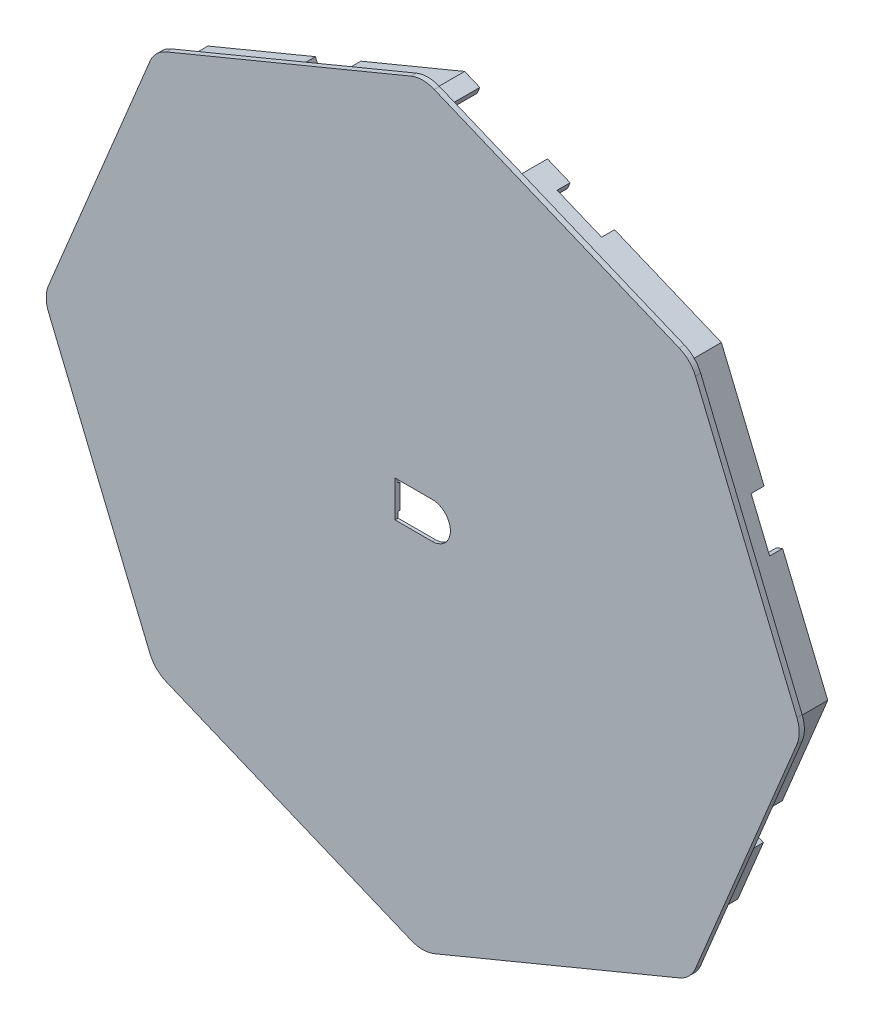
SolidWorks part; units mm, degrees
ref_plane "Plan de face" through (0, 0, 0) normal (0, 0, 1) x (1, 0, 0)
ref_plane "Plan de dessus" through (0, 0, 0) normal (0, 1, 0) x (1, 0, 0)
ref_plane "Plan de droite" through (0, 0, 0) normal (1, 0, 0) x (0, 0, -1)
sketch "Esquisse1" plane through (0, 0, 0) normal (0, 0, 1) x (1, 0, 0)
  line L0 (-19.5173, 52.6223) -> (-47.8358, 40.8923)
  line L5 (-49.73, 38.9982) -> (-61.46, 10.6796)
  line L6 (-61.46, 8.0008) -> (-49.73, -20.3178)
  line L7 (-47.8358, -22.212) -> (-19.5173, -33.9419)
  line L8 (-16.8385, -33.9419) -> (11.4801, -22.212)
  line L9 (13.3743, -20.3178) -> (25.1042, 8.0008)
  line L10 (25.1042, 10.6796) -> (13.3743, 38.9982)
  line L11 (11.4801, 40.8923) -> (-16.8385, 52.6223)
  arc A0 (-47.8358, 40.8923) -> (-49.73, 38.9982) centre (-46.4964, 37.6588) ccw
  arc A1 (-61.46, 10.6796) -> (-61.46, 8.0008) centre (-58.2264, 9.3402) ccw
  arc A2 (-49.73, -20.3178) -> (-47.8358, -22.212) centre (-46.4964, -18.9784) ccw
  arc A3 (-19.5173, -33.9419) -> (-16.8385, -33.9419) centre (-18.1779, -30.7083) ccw
  arc A4 (11.4801, -22.212) -> (13.3743, -20.3178) centre (10.1407, -18.9784) ccw
  arc A5 (25.1042, 8.0008) -> (25.1042, 10.6796) centre (21.8706, 9.3402) ccw
  arc A6 (13.3743, 38.9982) -> (11.4801, 40.8923) centre (10.1407, 37.6588) ccw
  arc A7 (-16.8385, 52.6223) -> (-19.5173, 52.6223) centre (-18.1779, 49.3887) ccw
extrude "Boss.-Extru.1" add sketch "Esquisse1" along normal blind 0.6
sketch "Esquisse3" plane through (0, 0, 0) normal (0, 0, -1) x (-1, 0, 0)
  line L63 (47.2618, 38.4241) -> (18.1779, 50.4711)
  line L64 (18.1779, 50.4711) -> (-10.9061, 38.4241)
  line L65 (-10.9061, 38.4241) -> (-22.953, 9.3402)
  line L66 (-22.953, 9.3402) -> (-10.9061, -19.7437)
  line L67 (-10.9061, -19.7437) -> (18.1779, -31.7907)
  line L68 (18.1779, -31.7907) -> (47.2618, -19.7437)
  line L69 (47.2618, -19.7437) -> (59.3088, 9.3402)
  line L70 (59.3088, 9.3402) -> (47.2618, 38.4241)
  line L71 (47.8741, 39.0364) -> (18.1779, 51.337)
  line L72 (60.1747, 9.3402) -> (47.8741, 39.0364)
  line L73 (47.8741, -20.356) -> (60.1747, 9.3402)
  line L74 (18.1779, -32.6566) -> (47.8741, -20.356)
  line L75 (-11.5184, -20.356) -> (18.1779, -32.6566)
  line L76 (-23.8189, 9.3402) -> (-11.5184, -20.356)
  line L77 (-11.5184, 39.0364) -> (-23.8189, 9.3402)
  line L78 (18.1779, 51.337) -> (-11.5184, 39.0364)
  line L79 (47.8741, 39.0364) -> (18.1779, 51.337)
  line L80 (60.1747, 9.3402) -> (47.8741, 39.0364)
  line L81 (47.8741, -20.356) -> (60.1747, 9.3402)
  line L82 (18.1779, -32.6566) -> (47.8741, -20.356)
  line L83 (-11.5184, -20.356) -> (18.1779, -32.6566)
  line L84 (-23.8189, 9.3402) -> (-11.5184, -20.356)
  line L85 (-11.5184, 39.0364) -> (-23.8189, 9.3402)
  line L86 (18.1779, 51.337) -> (-11.5184, 39.0364)
  dimension "D1" = 0.2
  dimension "D2" = 0.8
extrude "Boss.-Extru.2" add sketch "Esquisse3" along normal blind 4.25
sketch "Esquisse4" plane through (0, 0, 0) normal (0, 0, -1) x (-1, 0, 0)
  line L0 (17.7779, 6.6402) -> (17.7779, 12.0402) construction
  line L6 (21.1779, 6.6402) -> (14.3779, 6.6402) construction
  line L7 (14.3779, 12.0402) -> (21.1779, 12.0402) construction
  line L8 (14.3779, 6.6402) -> (14.3779, 12.0402) construction
  line L9 (21.3779, 6.4402) -> (14.1779, 6.4402)
  line L10 (21.3779, 6.4402) -> (21.3779, 12.2402)
  line L11 (21.3779, 12.2402) -> (14.1779, 12.2402)
  line L12 (14.1779, 6.4402) -> (14.1779, 12.2402)
  line L13 (21.3779, 6.4402) -> (14.1779, 12.2402) construction
  line L14 (21.3779, 12.2402) -> (14.1779, 6.4402) construction
  point P6 (17.7779, 9.3402)
  dimension "D1" = 0.2
  dimension "D2" = 0.2
extrude "Enlèv. mat.-Extru.2" cut sketch "Esquisse4" against normal blind 0.25
sketch "Esquisse2" plane through (0, 0, 0.6) normal (0, 0, 1) x (1, 0, 0)
  line L0 (-18.1779, -34.2083) -> (-18.1779, 52.8887) construction
  line L1 (-14.9779, 9.3402) -> (-21.3779, 9.3402) construction
  line L8 (-21.3779, 11.4402) -> (-17.0779, 11.4402)
  line L13 (-21.3779, 7.2402) -> (-17.0779, 7.2402)
  line L14 (-21.3779, 11.4402) -> (-21.3779, 7.2402)
  arc A0 (-19.5173, -33.9419) -> (-16.8385, -33.9419) centre (-18.1779, -30.7083) ccw construction
  arc A1 (-16.8385, 52.6223) -> (-19.5173, 52.6223) centre (-18.1779, 49.3887) ccw construction
  arc A9 (-17.0779, 11.4402) -> (-17.0779, 7.2402) centre (-17.0779, 9.3402) cw
extrude "Enlèv. mat.-Extru.1" cut sketch "Esquisse2" against normal blind 1
sketch "Esquisse5" plane through (15.4883, 37.392, 0) normal (0.3827, 0.9239, 0) x (0.9239, -0.3827, 0)
  line L1 (-26.0698, 0) -> (-34.542, 0)
  line L2 (-26.0698, 0) -> (-26.0698, 4.25)
  line L3 (-26.0698, 4.25) -> (-34.542, 4.25)
  line L4 (-34.542, 0) -> (-34.542, 4.25)
  line L5 (-36.44, 4.25) -> (-4.297, 4.25) construction
extrude "Enlèv. mat.-Extru.3" cut sketch "Esquisse5" against normal blind 1
sketch "Esquisse7" plane through (0, 0, -4.25) normal (0, 0, -1) x (-1, 0, 0)
  line L0 (-17.505, 21.4789) -> (-15.3414, 26.6549)
  line L1 (-17.505, 21.4789) -> (-18.939, 22.0784)
  line L2 (-15.3414, 26.6549) -> (-16.7754, 27.2543)
  line L3 (-18.939, 22.0784) -> (-16.7754, 27.2543)
  line L4 (-17.505, 21.4789) -> (-16.7754, 27.2543) construction
  line L5 (-15.3414, 26.6549) -> (-18.939, 22.0784) construction
  line L6 (18.1779, -33.7083) -> (18.1779, 52.3887) construction
  line L7 (-15.6405, -8.3138) -> (-17.8205, -3.0508)
  line L8 (-22.953, 9.3402) -> (-10.9061, -19.7437) construction
  line L9 (-17.8205, -3.0508) -> (-18.5596, -3.357)
  line L10 (-23.8189, 9.3402) -> (-11.5184, -20.356) construction
  line L11 (-18.5596, -3.357) -> (-16.3796, -8.6199)
  line L12 (-16.3796, -8.6199) -> (-15.6405, -8.3138)
  line L13 (6.6989, -27.036) -> (6.3928, -27.7751)
  line L14 (-10.9061, -19.7437) -> (18.1779, -31.7907) construction
  line L15 (-11.5184, -20.356) -> (18.1779, -32.6566) construction
  line L16 (6.3928, -27.7751) -> (1.1822, -25.6168)
  line L17 (1.1822, -25.6168) -> (1.4883, -24.8777)
  line L18 (1.4883, -24.8777) -> (6.6989, -27.036)
  line L19 (35.0484, -24.8027) -> (29.6568, -27.036)
  line L20 (18.1779, -31.7907) -> (47.2618, -19.7437) construction
  line L21 (29.6568, -27.036) -> (29.963, -27.7751)
  line L22 (18.1779, -32.6566) -> (47.8741, -20.356) construction
  line L23 (29.963, -27.7751) -> (35.3546, -25.5418)
  line L24 (35.3546, -25.5418) -> (35.0484, -24.8027)
  line L25 (52.1789, -7.8728) -> (52.918, -8.1789)
  line L26 (47.2618, -19.7437) -> (59.3088, 9.3402) construction
  line L27 (47.8741, -20.356) -> (60.1747, 9.3402) construction
  line L28 (52.918, -8.1789) -> (55.13, -2.8387)
  line L29 (55.13, -2.8387) -> (54.3909, -2.5326)
  line L30 (54.3909, -2.5326) -> (52.1789, -7.8728)
  line L31 (54.3213, 21.381) -> (55.0604, 21.6871)
  line L32 (59.3088, 9.3402) -> (47.2618, 38.4241) construction
  line L33 (60.1747, 9.3402) -> (47.8741, 39.0364) construction
  line L34 (55.0604, 21.6871) -> (52.8956, 26.9135)
  line L35 (52.8956, 26.9135) -> (52.1565, 26.6074)
  line L36 (52.1565, 26.6074) -> (54.3213, 21.381)
  line L37 (29.88, 45.6239) -> (30.1861, 46.363)
  line L38 (47.2618, 38.4241) -> (18.1779, 50.4711) construction
  line L39 (47.8741, 39.0364) -> (18.1779, 51.337) construction
  line L40 (30.1861, 46.363) -> (35.4331, 44.1896)
  line L41 (35.4331, 44.1896) -> (35.127, 43.4505)
  line L42 (35.127, 43.4505) -> (29.88, 45.6239)
  line L43 (6.2864, 45.5455) -> (5.9803, 46.2846)
  line L44 (8.9032, 46.6294) -> (-10.9061, 38.4241) construction
  line L45 (8.597, 47.3685) -> (-11.5184, 39.0364) construction
  line L46 (5.9803, 46.2846) -> (0.8379, 44.1546)
  line L47 (0.8379, 44.1546) -> (1.1441, 43.4155)
  line L48 (1.1441, 43.4155) -> (6.2864, 45.5455)
  point P1 (-17.1402, 24.3666)
  point P13 (18.1779, 9.3402)
extrude "Enlèv. mat.-Extru.4" cut sketch "Esquisse7" against normal blind 1.5
ref_plane "Plan1" through (16.846, -16.846, 0) normal (-0.7071, 0.7071, 0) x (0, 0, 1)
sketch "Esquisse8" plane through (16.846, -16.846, 0) normal (-0.7071, 0.7071, 0) x (0, 0, 1)
  line L6 (-0.2158, -1.666) -> (-4.45, -1.666)
  line L7 (-4.45, -10.766) -> (-4.45, -1.666)
  line L8 (-0.2158, -10.766) -> (-4.45, -10.766)
  line L9 (-0.2158, -10.766) -> (-0.2158, -1.666)
extrude "Enlèv. mat.-Extru.5" cut sketch "Esquisse8" along normal blind 5
sketch "Esquisse9" plane through (0, 0, -10) normal (0, 0, -1) x (-1, 0, 0)
  line L0 (-95.335, 117.5946) -> (-278.1174, 117.5946) construction
  line L1 (18.1779, -34.2495) -> (18.1779, 52.9299) construction
  line L2 (-25.4118, 9.3402) -> (61.7676, 9.3402) construction
  line L3 (-10.375, 4.3056) -> (-0.9298, 4.9699)
  line L4 (0, 5.9674) -> (0, 12.713)
  line L5 (-8.3173, -1.6814) -> (-1.1982, -0.2422)
  line L6 (0, -1.2224) -> (0, -12.2881)
  line L7 (15.377, 12.2209) -> (15.377, 6.4595)
  line L8 (0, 9.3402) -> (1.6274, 9.3402)
  line L9 (1.6274, 29.788) -> (1.6274, -11.1076)
  line L10 (1.9689, -11.8602) -> (2.4106, -12.2467)
  line L11 (3.8901, -12.065) -> (10.0273, -3.2398)
  line L12 (10.2064, -2.6689) -> (10.2064, 21.3493)
  line L13 (44.603, 5.5333) -> (7.788, -15.7985)
  line L14 (43.8776, 8.2733) -> (32.8856, 8.5506)
  line L15 (32.3569, 8.4149) -> (11.7348, -3.602)
  line L16 (11.3684, -3.9729) -> (5.8348, -13.7345)
  line L17 (17.1266, 5.3032) -> (21.1779, 8.2763)
  line L18 (21.1779, 12.0402) -> (21.1779, 6.6402) construction
  line L19 (36.6565, -1.0939) -> (45.9203, 3.9638)
  line L20 (36.3722, -2.6175) -> (40.9733, -8.0556)
  line L21 (30.0138, -4.7878) -> (24.1751, -8.1284)
  line L22 (23.7662, -9.4207) -> (27.7907, -18.0089)
  line L23 (31.325, -5.0757) -> (36.8392, -12.8188)
  line L24 (8.4389, -17.1929) -> (17.9866, -11.5351)
  line L25 (19.4327, -12.0443) -> (22.0647, -19.0641)
  line L26 (19.4327, 30.7247) -> (22.0647, 37.7445)
  line L27 (8.4389, 35.8733) -> (17.9866, 30.2155)
  line L28 (31.325, 23.7561) -> (36.8392, 31.4992)
  line L29 (23.7662, 28.1011) -> (27.7907, 36.6893)
  line L30 (30.0138, 23.4682) -> (24.1751, 26.8088)
  line L31 (36.3722, 21.2979) -> (40.9733, 26.736)
  line L32 (36.6565, 19.7743) -> (45.9203, 14.7166)
  line L33 (17.1266, 13.3772) -> (21.1779, 10.4041)
  line L34 (11.3684, 22.6533) -> (5.8348, 32.4149)
  line L35 (32.3569, 10.2655) -> (11.7348, 22.2824)
  line L36 (43.8776, 10.407) -> (32.8856, 10.1298)
  line L37 (44.603, 13.1471) -> (7.788, 34.4788)
  line L38 (3.8901, 30.7454) -> (10.0273, 21.9202)
  line L39 (1.9689, 30.5406) -> (2.4106, 30.9271)
  line L40 (0, 19.9028) -> (0, 30.9685)
  line L41 (-8.3173, 20.3618) -> (-1.1982, 18.9226)
  line L42 (-10.375, 14.3748) -> (-0.9298, 13.7105)
  arc A0 (17.0298, -34.0212) -> (19.3259, -34.0212) centre (18.1779, -31.2495) ccw construction
  arc A1 (19.3259, 52.7015) -> (17.0298, 52.7015) centre (18.1779, 49.9299) ccw construction
  circle A2 centre (18.1779, 9.3402) radius 38.1198
  circle A3 centre (18.1779, 9.3402) radius 33.6952
  circle A4 centre (18.1779, 9.3402) radius 31.7228
  arc A5 (-25.1835, 10.4882) -> (-25.1835, 8.1921) centre (-22.4118, 9.3402) ccw construction
  arc A6 (61.5392, 8.1921) -> (61.5392, 10.4882) centre (58.7676, 9.3402) ccw construction
  arc A7 (-9.0289, -3.0768) -> (-1.6634, -13.0364) centre (18.1779, 9.3402) ccw
  arc A8 (-11.4354, 13.5169) -> (-11.4354, 5.1635) centre (18.1779, 9.3402) ccw
  arc A9 (-10.375, 4.3056) -> (-11.4354, 5.1635) centre (-10.4452, 5.3032) cw
  arc A10 (-0.9298, 4.9699) -> (0, 5.9674) centre (-1, 5.9674) ccw
  arc A11 (-1.1982, -0.2422) -> (0, -1.2224) centre (-1, -1.2224) cw
  arc A12 (-8.3173, -1.6814) -> (-9.0289, -3.0768) centre (-8.1191, -2.6616) ccw
  arc A13 (10.0273, -3.2398) -> (10.2064, -2.6689) centre (9.2064, -2.6689) ccw
  arc A14 (1.6274, -11.1076) -> (1.9689, -11.8602) centre (2.6274, -11.1076) ccw
  arc A15 (2.4106, -12.2467) -> (3.8901, -12.065) centre (3.0691, -11.4941) ccw
  arc A16 (5.71, -14.1252) -> (7.1981, -15.9293) centre (7.3436, -14.2935) ccw
  arc A17 (44.5359, 8.0037) -> (45.0671, 6.1381) centre (43.2486, 6.6287) cw
  arc A18 (15.377, 6.4595) -> (17.1266, 5.3032) centre (15.4452, 4.6608) ccw
  arc A19 (21.1779, 8.2763) -> (25.8249, 9.3402) centre (23.3751, 9.36) ccw
  circle A20 centre (40.1415, -10.4161) radius 4.1998 construction
  arc A21 (8.6295, -19.0009) -> (21.2304, -20.4099) centre (18.1779, 9.3402) ccw
  arc A22 (29.0601, -18.516) -> (36.6421, -14.1856) centre (18.1779, 9.3402) ccw
  arc A23 (42.5517, -7.9892) -> (47.3758, 2.8697) centre (18.1779, 9.3402) ccw
  arc A24 (11.7348, -3.602) -> (11.3684, -3.9729) centre (12.2383, -4.466) ccw
  arc A25 (7.788, -15.7985) -> (7.1981, -15.9293) centre (7.2867, -14.9332) cw
  arc A26 (5.8348, -13.7345) -> (5.71, -14.1252) centre (6.7047, -14.2276) ccw
  arc A27 (44.603, 5.5333) -> (45.0671, 6.1381) centre (44.1016, 6.3986) ccw
  arc A28 (44.5359, 8.0037) -> (43.8776, 8.2733) centre (43.8524, 7.2737) ccw
  arc A29 (32.8856, 8.5506) -> (32.3569, 8.4149) centre (32.8604, 7.5509) ccw
  arc A30 (0, -12.2881) -> (-1.6634, -13.0364) centre (-1, -12.2881) cw
  arc A31 (45.9203, 3.9638) -> (47.3758, 2.8697) centre (46.3995, 3.0861) cw
  arc A32 (36.6565, -1.0939) -> (36.3722, -2.6175) centre (37.1357, -1.9716) ccw
  arc A33 (40.9733, -8.0556) -> (42.5517, -7.9892) centre (41.7367, -7.4097) ccw
  arc A34 (36.8392, -12.8188) -> (36.6421, -14.1856) centre (36.0247, -13.3989) cw
  arc A35 (30.0138, -4.7878) -> (31.325, -5.0757) centre (30.5104, -5.6558) cw
  arc A36 (24.1751, -8.1284) -> (23.7662, -9.4207) centre (24.6717, -8.9964) ccw
  arc A37 (27.7907, -18.0089) -> (29.0601, -18.516) centre (28.6962, -17.5845) ccw
  arc A38 (22.0647, -19.0641) -> (21.2304, -20.4099) centre (21.1283, -19.4152) cw
  arc A39 (17.9866, -11.5351) -> (19.4327, -12.0443) centre (18.4964, -12.3954) cw
  arc A40 (8.4389, -17.1929) -> (8.6295, -19.0009) centre (8.9488, -18.0532) ccw
  arc A41 (8.4389, 35.8733) -> (8.6295, 37.6813) centre (8.9488, 36.7336) cw
  arc A42 (17.9866, 30.2155) -> (19.4327, 30.7247) centre (18.4964, 31.0757) ccw
  arc A43 (22.0647, 37.7445) -> (21.2304, 39.0903) centre (21.1283, 38.0956) ccw
  arc A44 (27.7907, 36.6893) -> (29.0601, 37.1964) centre (28.6962, 36.2649) cw
  arc A45 (24.1751, 26.8088) -> (23.7662, 28.1011) centre (24.6717, 27.6768) cw
  arc A46 (30.0138, 23.4682) -> (31.325, 23.7561) centre (30.5104, 24.3362) ccw
  arc A47 (36.8392, 31.4992) -> (36.6421, 32.866) centre (36.0247, 32.0793) ccw
  arc A48 (40.9733, 26.736) -> (42.5517, 26.6695) centre (41.7367, 26.0901) cw
  arc A49 (36.6565, 19.7743) -> (36.3722, 21.2979) centre (37.1357, 20.652) cw
  arc A50 (45.9203, 14.7166) -> (47.3758, 15.8107) centre (46.3995, 15.5943) ccw
  arc A51 (0, 30.9685) -> (-1.6634, 31.7168) centre (-1, 30.9685) ccw
  arc A52 (32.8856, 10.1298) -> (32.3569, 10.2655) centre (32.8604, 11.1295) cw
  arc A53 (44.5359, 10.6767) -> (43.8776, 10.407) centre (43.8524, 11.4067) cw
  arc A54 (44.603, 13.1471) -> (45.0671, 12.5422) centre (44.1016, 12.2818) cw
  arc A55 (5.8348, 32.4149) -> (5.71, 32.8056) centre (6.7047, 32.908) cw
  arc A56 (7.788, 34.4788) -> (7.1981, 34.6097) centre (7.2867, 33.6136) ccw
  arc A57 (11.7348, 22.2824) -> (11.3684, 22.6533) centre (12.2383, 23.1464) cw
  arc A58 (42.5517, 26.6695) -> (47.3758, 15.8107) centre (18.1779, 9.3402) cw
  arc A59 (29.0601, 37.1964) -> (36.6421, 32.866) centre (18.1779, 9.3402) cw
  arc A60 (8.6295, 37.6813) -> (21.2304, 39.0903) centre (18.1779, 9.3402) cw
  arc A61 (21.1779, 10.4041) -> (25.8249, 9.3402) centre (23.3751, 9.3204) cw
  arc A62 (15.377, 12.2209) -> (17.1266, 13.3772) centre (15.4452, 14.0196) cw
  arc A63 (44.5359, 10.6767) -> (45.0671, 12.5422) centre (43.2486, 12.0517) ccw
  arc A64 (5.71, 32.8056) -> (7.1981, 34.6097) centre (7.3436, 32.9738) cw
  arc A65 (2.4106, 30.9271) -> (3.8901, 30.7454) centre (3.0691, 30.1745) cw
  arc A66 (1.6274, 29.788) -> (1.9689, 30.5406) centre (2.6274, 29.788) cw
  arc A67 (10.0273, 21.9202) -> (10.2064, 21.3493) centre (9.2064, 21.3493) cw
  arc A68 (-8.3173, 20.3618) -> (-9.0289, 21.7572) centre (-8.1191, 21.342) cw
  arc A69 (-1.1982, 18.9226) -> (0, 19.9028) centre (-1, 19.9028) ccw
  arc A70 (-0.9298, 13.7105) -> (0, 12.713) centre (-1, 12.713) cw
  arc A71 (-10.375, 14.3748) -> (-11.4354, 13.5169) centre (-10.4452, 13.3772) ccw
  arc A72 (-9.0289, 21.7572) -> (-1.6634, 31.7168) centre (18.1779, 9.3402) cw
  point P30 (10.2064, 9.3402)
  point P38 (15.377, 9.3402)
  point P45 (0, 0)
  point P61 (6.648, 36.9346)
  point P98 (47.7632, 4.9699)
  point P103 (41.787, -9.0174)
  point P106 (37.384, -13.5839)
  point P113 (28.1817, -18.8433)
  point P116 (22.5096, -20.2508)
  point P121 (6.648, -18.2542)
  point P200 (22.5096, 38.9312)
  point P201 (28.1817, 37.5237)
  point P202 (37.384, 32.2642)
  point P203 (41.787, 27.6977)
  point P204 (47.7632, 13.7105)
  point P205 (0, 18.6804)
  dimension "D1" = 1
  dimension "D2" = 1
  dimension "D3" = 1
sketch "Esquisse10" plane through (0, 0, 0) normal (0, 0, -1) x (-1, 0, 0)
  line L0 (18.1779, -32.6566) -> (18.1779, 51.337) construction
  line L1 (18.1779, -34.2495) -> (18.1779, 52.9299) construction
  line L2 (-25.4118, 9.3402) -> (61.7676, 9.3402) construction
  line L3 (-10.375, 4.3056) -> (-0.9298, 4.9699)
  line L4 (0, 5.9674) -> (0, 12.713)
  line L5 (-8.3173, -1.6814) -> (-1.1982, -0.2422)
  line L6 (0, -1.2224) -> (0, -12.2881)
  line L7 (15.377, 12.2209) -> (15.377, 6.4595)
  line L8 (0, 9.3402) -> (1.6274, 9.3402)
  line L9 (1.6274, 29.788) -> (1.6274, -11.1076)
  line L10 (1.9689, -11.8602) -> (2.4106, -12.2467)
  line L11 (3.8901, -12.065) -> (10.0273, -3.2398)
  line L12 (10.2064, -2.6689) -> (10.2064, 21.3493)
  line L13 (44.603, 5.5333) -> (7.788, -15.7985)
  line L14 (43.8776, 8.2733) -> (32.8856, 8.5506)
  line L15 (32.3569, 8.4149) -> (11.7348, -3.602)
  line L16 (11.3684, -3.9729) -> (5.8348, -13.7345)
  line L17 (17.1266, 5.3032) -> (21.9458, 8.2657)
  line L18 (36.6565, -1.0939) -> (45.9203, 3.9638)
  line L19 (36.3722, -2.6175) -> (40.9733, -8.0556)
  line L20 (30.0138, -4.7878) -> (24.1751, -8.1284)
  line L21 (23.7662, -9.4207) -> (27.7907, -18.0089)
  line L22 (31.325, -5.0757) -> (36.8392, -12.8188)
  line L23 (8.4389, -17.1929) -> (17.9866, -11.5351)
  line L24 (19.4327, -12.0443) -> (22.0647, -19.0641)
  line L25 (19.4327, 30.7247) -> (22.0647, 37.7445)
  line L26 (8.4389, 35.8733) -> (17.9866, 30.2155)
  line L27 (31.325, 23.7561) -> (36.8392, 31.4992)
  line L28 (23.7662, 28.1011) -> (27.7907, 36.6893)
  line L29 (30.0138, 23.4682) -> (24.1751, 26.8088)
  line L30 (36.3722, 21.2979) -> (40.9733, 26.736)
  line L31 (36.6565, 19.7743) -> (45.9203, 14.7166)
  line L32 (17.1266, 13.3772) -> (21.9458, 10.4147)
  line L33 (11.3684, 22.6533) -> (5.8348, 32.4149)
  line L34 (32.3569, 10.2655) -> (11.7348, 22.2824)
  line L35 (43.8776, 10.407) -> (32.8856, 10.1298)
  line L36 (44.603, 13.1471) -> (7.788, 34.4788)
  line L37 (3.8901, 30.7454) -> (10.0273, 21.9202)
  line L38 (1.9689, 30.5406) -> (2.4106, 30.9271)
  line L39 (0, 19.9028) -> (0, 30.9685)
  line L40 (-8.3173, 20.3618) -> (-1.1982, 18.9226)
  line L41 (-10.375, 14.3748) -> (-0.9298, 13.7105)
  circle A0 centre (18.1779, 9.3402) radius 37
  circle A1 centre (18.1779, 9.3402) radius 33.6952
  circle A2 centre (18.1779, 9.3402) radius 31.7228
  arc A3 (-9.0289, -3.0768) -> (-1.6634, -13.0364) centre (18.1779, 9.3402) ccw
  arc A4 (-11.4354, 13.5169) -> (-11.4354, 5.1635) centre (18.1779, 9.3402) ccw
  arc A5 (-10.375, 4.3056) -> (-11.4354, 5.1635) centre (-10.4452, 5.3032) cw
  arc A6 (-0.9298, 4.9699) -> (0, 5.9674) centre (-1, 5.9674) ccw
  arc A7 (-1.1982, -0.2422) -> (0, -1.2224) centre (-1, -1.2224) cw
  arc A8 (-8.3173, -1.6814) -> (-9.0289, -3.0768) centre (-8.1191, -2.6616) ccw
  arc A9 (10.0273, -3.2398) -> (10.2064, -2.6689) centre (9.2064, -2.6689) ccw
  arc A10 (1.6274, -11.1076) -> (1.9689, -11.8602) centre (2.6274, -11.1076) ccw
  arc A11 (2.4106, -12.2467) -> (3.8901, -12.065) centre (3.0691, -11.4941) ccw
  arc A12 (5.71, -14.1252) -> (7.1981, -15.9293) centre (7.3436, -14.2935) ccw
  arc A13 (44.5359, 8.0037) -> (45.0671, 6.1381) centre (43.2486, 6.6287) cw
  arc A14 (15.377, 6.4595) -> (17.1266, 5.3032) centre (15.4452, 4.6608) ccw
  arc A15 (21.9458, 8.2657) -> (25.1749, 9.3402) centre (23.3751, 9.36) ccw
  arc A16 (8.6295, -19.0009) -> (21.2304, -20.4099) centre (18.1779, 9.3402) ccw
  arc A17 (29.0601, -18.516) -> (36.6421, -14.1856) centre (18.1779, 9.3402) ccw
  arc A18 (42.5517, -7.9892) -> (47.3758, 2.8697) centre (18.1779, 9.3402) ccw
  arc A19 (11.7348, -3.602) -> (11.3684, -3.9729) centre (12.2383, -4.466) ccw
  arc A20 (7.788, -15.7985) -> (7.1981, -15.9293) centre (7.2867, -14.9332) cw
  arc A21 (5.8348, -13.7345) -> (5.71, -14.1252) centre (6.7047, -14.2276) ccw
  arc A22 (44.603, 5.5333) -> (45.0671, 6.1381) centre (44.1016, 6.3986) ccw
  arc A23 (44.5359, 8.0037) -> (43.8776, 8.2733) centre (43.8524, 7.2737) ccw
  arc A24 (32.8856, 8.5506) -> (32.3569, 8.4149) centre (32.8604, 7.5509) ccw
  arc A25 (0, -12.2881) -> (-1.6634, -13.0364) centre (-1, -12.2881) cw
  arc A26 (45.9203, 3.9638) -> (47.3758, 2.8697) centre (46.3995, 3.0861) cw
  arc A27 (36.6565, -1.0939) -> (36.3722, -2.6175) centre (37.1357, -1.9716) ccw
  arc A28 (40.9733, -8.0556) -> (42.5517, -7.9892) centre (41.7367, -7.4097) ccw
  arc A29 (36.8392, -12.8188) -> (36.6421, -14.1856) centre (36.0247, -13.3989) cw
  arc A30 (30.0138, -4.7878) -> (31.325, -5.0757) centre (30.5104, -5.6558) cw
  arc A31 (24.1751, -8.1284) -> (23.7662, -9.4207) centre (24.6717, -8.9964) ccw
  arc A32 (27.7907, -18.0089) -> (29.0601, -18.516) centre (28.6962, -17.5845) ccw
  arc A33 (22.0647, -19.0641) -> (21.2304, -20.4099) centre (21.1283, -19.4152) cw
  arc A34 (17.9866, -11.5351) -> (19.4327, -12.0443) centre (18.4964, -12.3954) cw
  arc A35 (8.4389, -17.1929) -> (8.6295, -19.0009) centre (8.9488, -18.0532) ccw
  arc A36 (8.4389, 35.8733) -> (8.6295, 37.6813) centre (8.9488, 36.7336) cw
  arc A37 (17.9866, 30.2155) -> (19.4327, 30.7247) centre (18.4964, 31.0757) ccw
  arc A38 (22.0647, 37.7445) -> (21.2304, 39.0903) centre (21.1283, 38.0956) ccw
  arc A39 (27.7907, 36.6893) -> (29.0601, 37.1964) centre (28.6962, 36.2649) cw
  arc A40 (24.1751, 26.8088) -> (23.7662, 28.1011) centre (24.6717, 27.6768) cw
  arc A41 (30.0138, 23.4682) -> (31.325, 23.7561) centre (30.5104, 24.3362) ccw
  arc A42 (36.8392, 31.4992) -> (36.6421, 32.866) centre (36.0247, 32.0793) ccw
  arc A43 (40.9733, 26.736) -> (42.5517, 26.6695) centre (41.7367, 26.0901) cw
  arc A44 (36.6565, 19.7743) -> (36.3722, 21.2979) centre (37.1357, 20.652) cw
  arc A45 (45.9203, 14.7166) -> (47.3758, 15.8107) centre (46.3995, 15.5943) ccw
  arc A46 (0, 30.9685) -> (-1.6634, 31.7168) centre (-1, 30.9685) ccw
  arc A47 (32.8856, 10.1298) -> (32.3569, 10.2655) centre (32.8604, 11.1295) cw
  arc A48 (44.5359, 10.6767) -> (43.8776, 10.407) centre (43.8524, 11.4067) cw
  arc A49 (44.603, 13.1471) -> (45.0671, 12.5422) centre (44.1016, 12.2818) cw
  arc A50 (5.8348, 32.4149) -> (5.71, 32.8056) centre (6.7047, 32.908) cw
  arc A51 (7.788, 34.4788) -> (7.1981, 34.6097) centre (7.2867, 33.6136) ccw
  arc A52 (11.7348, 22.2824) -> (11.3684, 22.6533) centre (12.2383, 23.1464) cw
  arc A53 (42.5517, 26.6695) -> (47.3758, 15.8107) centre (18.1779, 9.3402) cw
  arc A54 (29.0601, 37.1964) -> (36.6421, 32.866) centre (18.1779, 9.3402) cw
  arc A55 (8.6295, 37.6813) -> (21.2304, 39.0903) centre (18.1779, 9.3402) cw
  arc A56 (21.9458, 10.4147) -> (25.1749, 9.3402) centre (23.3751, 9.3204) cw
  arc A57 (15.377, 12.2209) -> (17.1266, 13.3772) centre (15.4452, 14.0196) cw
  arc A58 (44.5359, 10.6767) -> (45.0671, 12.5422) centre (43.2486, 12.0517) ccw
  arc A59 (5.71, 32.8056) -> (7.1981, 34.6097) centre (7.3436, 32.9738) cw
  arc A60 (2.4106, 30.9271) -> (3.8901, 30.7454) centre (3.0691, 30.1745) cw
  arc A61 (1.6274, 29.788) -> (1.9689, 30.5406) centre (2.6274, 29.788) cw
  arc A62 (10.0273, 21.9202) -> (10.2064, 21.3493) centre (9.2064, 21.3493) cw
  arc A63 (-8.3173, 20.3618) -> (-9.0289, 21.7572) centre (-8.1191, 21.342) cw
  arc A64 (-1.1982, 18.9226) -> (0, 19.9028) centre (-1, 19.9028) ccw
  arc A65 (-0.9298, 13.7105) -> (0, 12.713) centre (-1, 12.713) cw
  arc A66 (-10.375, 14.3748) -> (-11.4354, 13.5169) centre (-10.4452, 13.3772) ccw
  arc A67 (-9.0289, 21.7572) -> (-1.6634, 31.7168) centre (18.1779, 9.3402) cw
  point P18 (10.2064, 9.3402)
  point P26 (15.377, 9.3402)
  point P48 (6.648, 36.9346)
  point P176 (22.5096, 38.9312)
  point P177 (28.1817, 37.5237)
  point P178 (37.384, 32.2642)
  point P179 (41.787, 27.6977)
  point P180 (47.7632, 13.7105)
  point P181 (0, 18.6804)
  dimension "D1" = 1
  dimension "D2" = 1
  dimension "D3" = 1
extrude "Enlèv. mat.-Extru.6" cut sketch "Esquisse10" against normal blind 0.25
